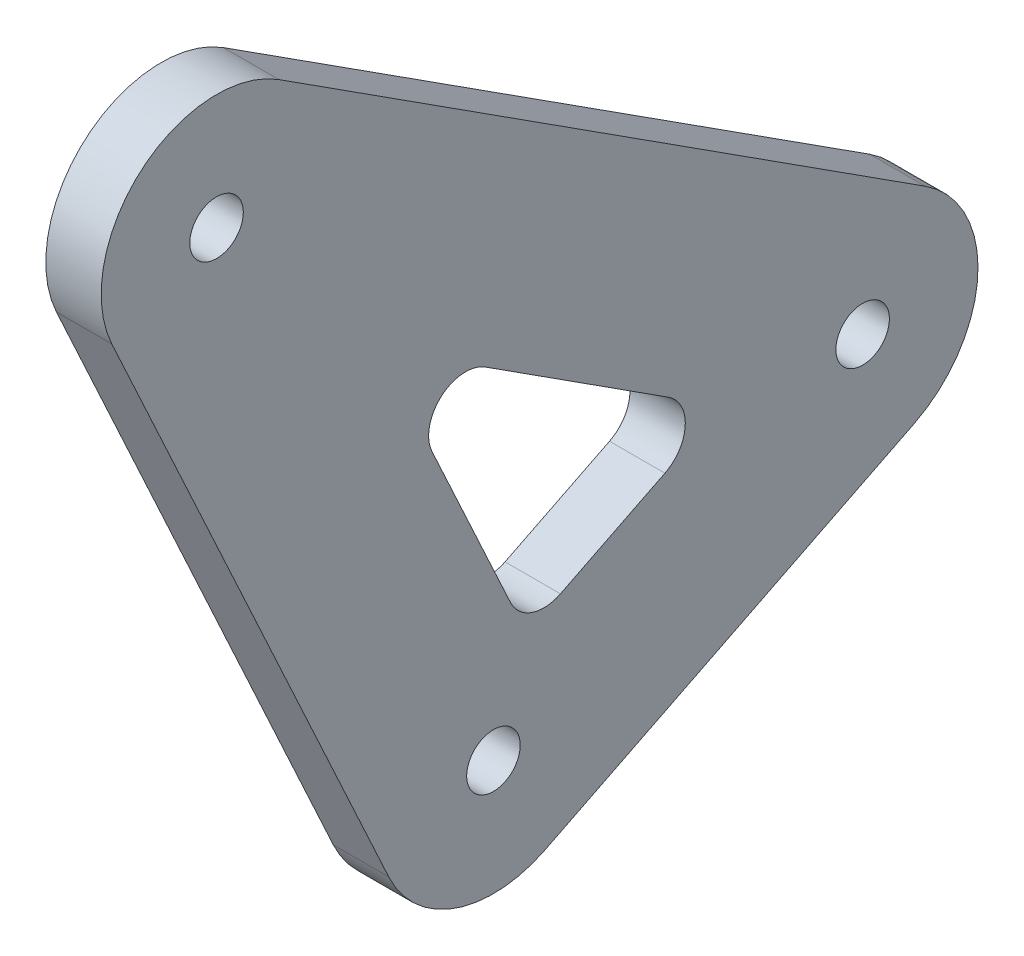
SolidWorks part; units mm, degrees
ref_plane "Front Plane" through (0, 0, 0) normal (0, 0, 1) x (1, 0, 0)
ref_plane "Top Plane" through (0, 0, 0) normal (0, 1, 0) x (1, 0, 0)
ref_plane "Right Plane" through (0, 0, 0) normal (1, 0, 0) x (0, 0, -1)
sketch "Sketch1" plane through (0, 0, 0) normal (1, 0, 0) x (0, 0, -1)
  line L0 (0, 0) -> (20, 10) construction
  line L1 (20, 10) -> (-15, 32.5) construction
  line L2 (-15, 32.5) -> (0, 0) construction
  line L3 (-20.6747, 29.8809) -> (-5.6747, -2.6191)
  line L4 (2.7951, -5.5902) -> (22.7951, 4.4098)
  line L5 (-11.6203, 37.7574) -> (23.3797, 15.2574)
  line L6 (0, 0) -> (20, 0) construction
  line L7 (20, 0) -> (20, 10) construction
  circle A0 centre (-15, 32.5) radius 1.45
  circle A1 centre (0, 0) radius 1.45
  circle A2 centre (20, 10) radius 1.45
  circle A3 centre (-15, 32.5) radius 6.25
  circle A4 centre (20, 10) radius 6.25
  circle A5 centre (0, 0) radius 6.25
  dimension "D3" = 2.9
  dimension "D4" = 12.5
  dimension "D1" = 10
  dimension "D2" = 15
  dimension "D5" = 20
  dimension "D6" = 32.5
extrude "Boss-Extrude1" add sketch "Sketch1" along normal mid plane 3
sketch "Sketch2" plane through (1.5, 0, 0) normal (1, 0, 0) x (0, 0, -1)
  line L0 (-15, 32.5) -> (20, 10) construction
  line L1 (2.5, 21.25) -> (1.9592, 20.4088) construction
  line L5 (12.474, 13.6494) -> (8.5535, 7.5508) construction
  line L21 (1.7835, 5.0844) -> (12.4307, 10.408)
  line L22 (-6.2019, 22.386) -> (1.7835, 5.0844)
  line L23 (12.4307, 10.408) -> (-6.2019, 22.386)
  line L24 (3.6291, 6.0072) -> (9.2881, 8.8367)
  line L25 (-3.3255, 16.1538) -> (0.9188, 6.9579)
  line L26 (9.4752, 12.3079) -> (-0.428, 18.6743)
  arc A11 (9.2881, 8.8367) -> (9.4752, 12.3079) centre (8.3937, 10.6255) ccw
  arc A12 (3.6291, 6.0072) -> (0.9188, 6.9579) centre (2.7347, 7.796) cw
  arc A13 (-3.3255, 16.1538) -> (-0.428, 18.6743) centre (-1.5095, 16.9919) cw
  dimension "D2" = 2
  dimension "D1" = 10
extrude "Cut-Extrude1" cut sketch "Sketch2" against normal blind 3
